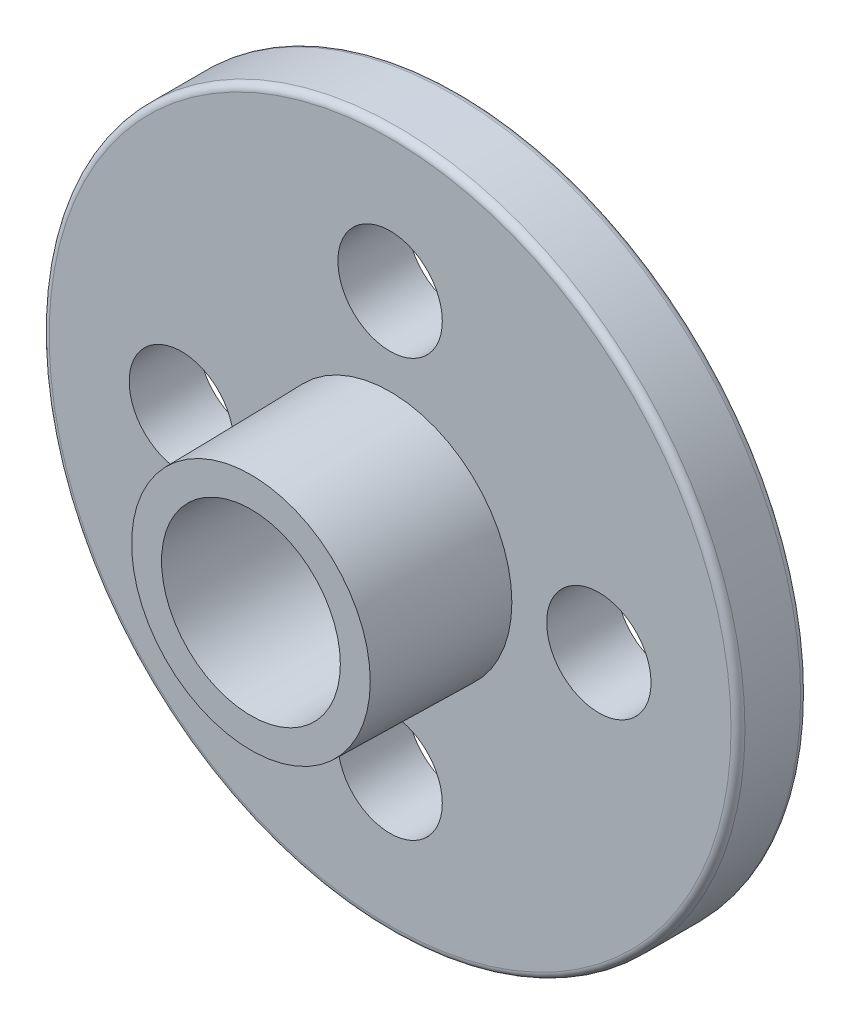
SolidWorks part; units mm, degrees
ref_plane "Ön Düzlem" through (0, 0, 0) normal (0, 0, 1) x (1, 0, 0)
ref_plane "Üst Düzlem" through (0, 0, 0) normal (0, 1, 0) x (1, 0, 0)
ref_plane "Sağ Düzlem" through (0, 0, 0) normal (1, 0, 0) x (0, 0, -1)
sketch "Çizim1" plane through (0, 0, 0) normal (0, 0, 1) x (1, 0, 0)
  line L0 (0, 10) -> (0, -10) construction
  line L1 (-10, 0) -> (10, 0) construction
  circle A0 centre (0, 0) radius 10
  circle A1 centre (0, 6) radius 1.5
  circle A2 centre (6, 0) radius 1.5
  circle A3 centre (0, -6) radius 1.5
  circle A4 centre (-6, 0) radius 1.5
  point P18 (0, 0)
  dimension "D1" = 20
  dimension "D2" = 3
  dimension "D3" = 6
  dimension "D4" = 4
extrude "Yükseklik-Ekstrüzyon1" add sketch "Çizim1" along normal blind 2
fillet "Radyus1" radius 0.2 2 edges at (10, 0, 0) (10, 0, 2)
sketch "Çizim2" plane through (0, 0, 2) normal (0, 0, 1) x (1, 0, 0)
  circle A0 centre (0, 0) radius 2.5
  circle A1 centre (0, 0) radius 3.5
  dimension "D1" = 7
  dimension "D2" = 5
extrude "Yükseklik-Ekstrüzyon2" add sketch "Çizim2" along normal blind 4 draft 1
sketch "Çizim3" plane through (0, 0, 0) normal (0, 0, -1) x (-1, 0, 0)
  circle A0 centre (0, 0) radius 1.5
  dimension "D1" = 3
extrude "Kes-Ekstrüzyon1" cut sketch "Çizim3" against normal blind 4
